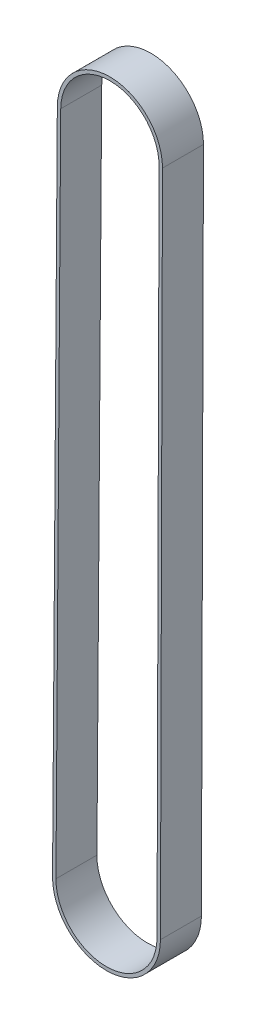
SolidWorks part; units mm, degrees
ref_plane "Front Plane" through (0, 0, 0) normal (0, 0, 1) x (1, 0, 0)
ref_plane "Top Plane" through (0, 0, 0) normal (0, 1, 0) x (1, 0, 0)
ref_plane "Right Plane" through (0, 0, 0) normal (1, 0, 0) x (0, 0, -1)
sketch "Sketch2" plane through (0, 0, 0) normal (0, 0, 1) x (1, 0, 0)
  line L0 (0, 0) -> (1, 0) construction
  line L1 (0, 0) -> (0, 1) construction
  line L2 (7.2, -2.822) -> (6.9, -100.8227)
  line L3 (-7.8998, -100.7471) -> (-7.1998, -2.7486)
  arc A0 (-7.1998, -2.7486) -> (7.2, -2.822) centre (0, -2.8) cw
  arc A1 (6.9, -100.8227) -> (-7.8998, -100.7471) centre (-0.5, -100.8) cw
extrude "Extrude-Thin1" add sketch "Sketch2" along normal blind 6 from offset 0.25 thin thin type one direction wall 0.5
